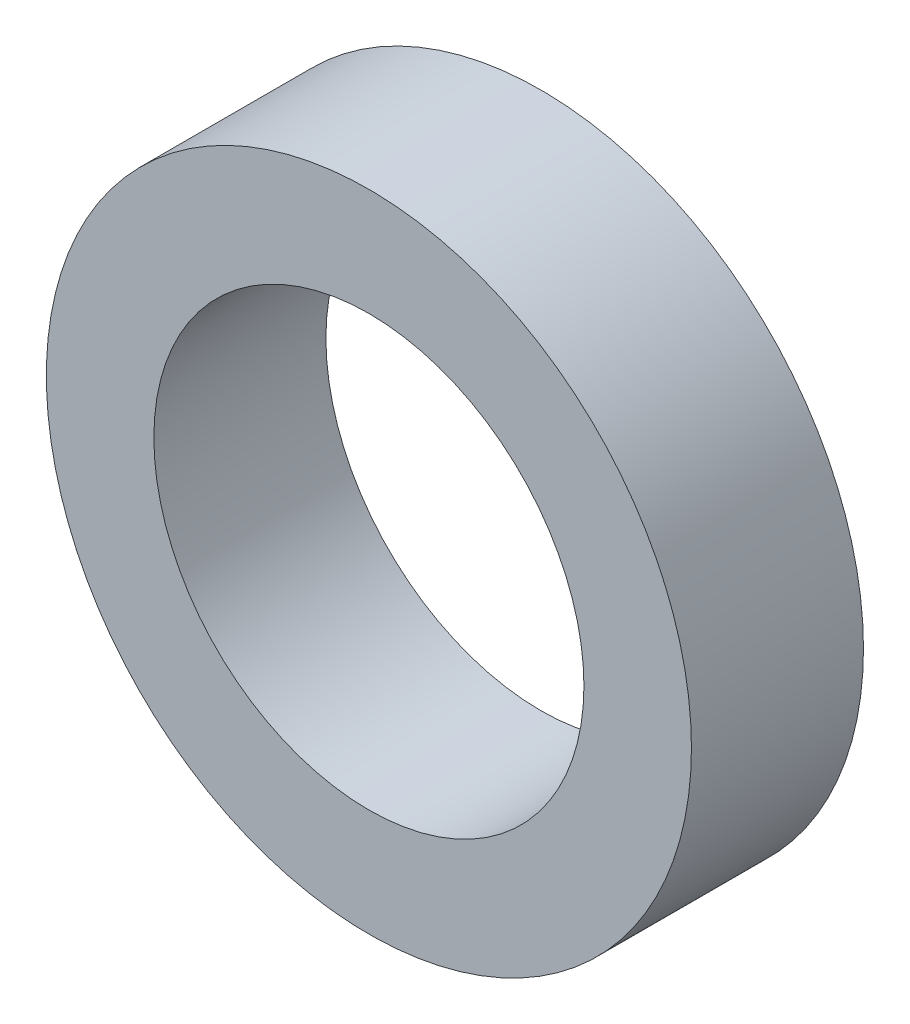
SolidWorks part; units mm, degrees
ref_plane "前视基准面" through (0, 0, 0) normal (0, 0, 1) x (1, 0, 0)
ref_plane "上视基准面" through (0, 0, 0) normal (0, 1, 0) x (1, 0, 0)
ref_plane "右视基准面" through (0, 0, 0) normal (1, 0, 0) x (0, 0, -1)
sketch "草图1" plane through (0, 0, 0) normal (0, 0, 1) x (1, 0, 0)
  circle A0 centre (0, 0) radius 5
  circle A1 centre (0, 0) radius 7.5
  dimension "D1" = 15
  dimension "D2" = 10
extrude "凸台-拉伸1" add sketch "草图1" along normal blind 4
